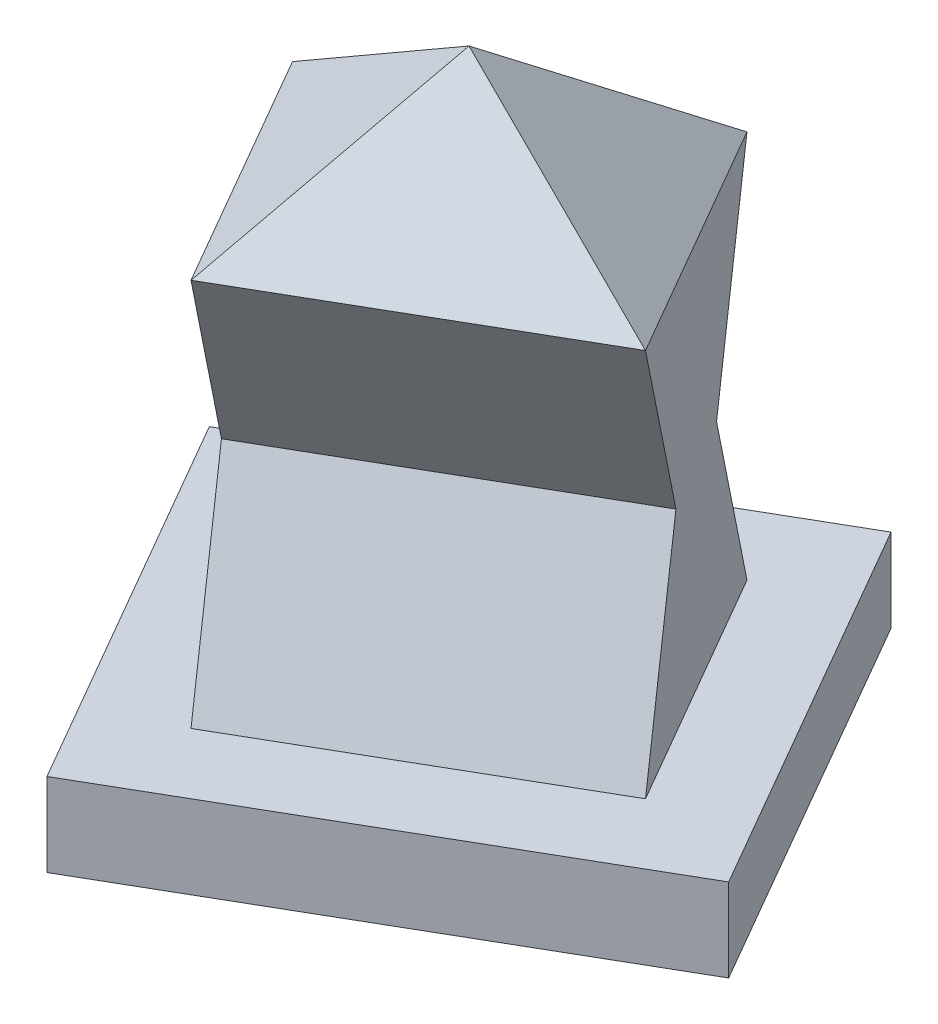
SolidWorks part; units mm, degrees
other "Perspective"
ref_plane "Front" through (0, 0, 0) normal (0, 0, 1) x (1, 0, 0)
ref_plane "Top" through (0, 0, 0) normal (0, 1, 0) x (1, 0, 0)
ref_plane "Right" through (0, 0, 0) normal (1, 0, 0) x (0, 0, -1)
sketch "Sketch1" plane through (0, 0, 0) normal (0, 1, 0) x (1, 0, 0)
  line L0 (-58.9711, 12.141) -> (18.9711, 57.141)
  line L1 (18.9711, 57.141) -> (58.9711, -12.141)
  line L2 (58.9711, -12.141) -> (-18.9711, -57.141)
  line L3 (-18.9711, -57.141) -> (-58.9711, 12.141)
  line L4 (58.9711, -12.141) -> (-58.9711, 12.141) construction
  line L5 (18.9711, 57.141) -> (-8.9014, 57.141) construction
  dimension "D1" = 30
  dimension "D2" = 80
  dimension "D3" = 90
  dimension "D4" = 57.141
extrude "Extrude1" add sketch "Sketch1" along normal blind 15
sketch "Sketch2" plane through (0, 15, 0) normal (0, 1, 0) x (-1, 0, 0)
  line L0 (38.4808, -6.6506) -> (-13.4808, -36.6506)
  line L1 (-13.4808, -36.6506) -> (-38.4808, 6.6506)
  line L2 (-38.4808, 6.6506) -> (13.4808, 36.6506)
  line L3 (13.4808, 36.6506) -> (38.4808, -6.6506)
  line L4 (-18.9711, -57.141) -> (58.9711, -12.141) construction
  line L5 (-58.9711, 12.141) -> (-18.9711, -57.141) construction
  line L6 (58.9711, -12.141) -> (18.9711, 57.141) construction
  line L7 (18.9711, 57.141) -> (-58.9711, 12.141) construction
  dimension "D1" = 15
  dimension "D2" = 15
  dimension "D3" = 15
  dimension "D4" = 15
extrude "Extrude2" add sketch "Sketch2" along normal blind 70
sketch "Sketch3" plane through (-25.9808, 0, 15) normal (-0.866, 0, 0.5) x (0.5, 0, 0.866)
  line L0 (-25, 15) -> (-25, 85)
  line L1 (-25, 85) -> (-10, 50)
  line L2 (-10, 50) -> (-25, 15)
  line L3 (25, 85) -> (25, 15)
  line L4 (25, 15) -> (10, 50)
  line L5 (10, 50) -> (25, 85)
  dimension "D1" = 20
extrude "Cut-Extrude1" cut sketch "Sketch3" against normal blind 60
sketch "Sketch4" plane through (0, 85, 0) normal (0, 1, 0) x (-1, 0, 0)
  line L0 (38.4808, -6.6506) -> (-13.4808, -36.6506)
  line L1 (-13.4808, -36.6506) -> (-38.4808, 6.6506)
  line L2 (-38.4808, 6.6506) -> (13.4808, 36.6506)
  line L3 (13.4808, 36.6506) -> (38.4808, -6.6506)
sketch "Sketch5" plane through (0, 0, 0) normal (0, 0, 1) x (1, 0, 0)
  line L0 (-38.4808, 85) -> (13.4808, 85) construction
  point P0 (0, 110)
  dimension "D1" = 25
loft "Loft1" add profiles "Sketch4", "Sketch5"
